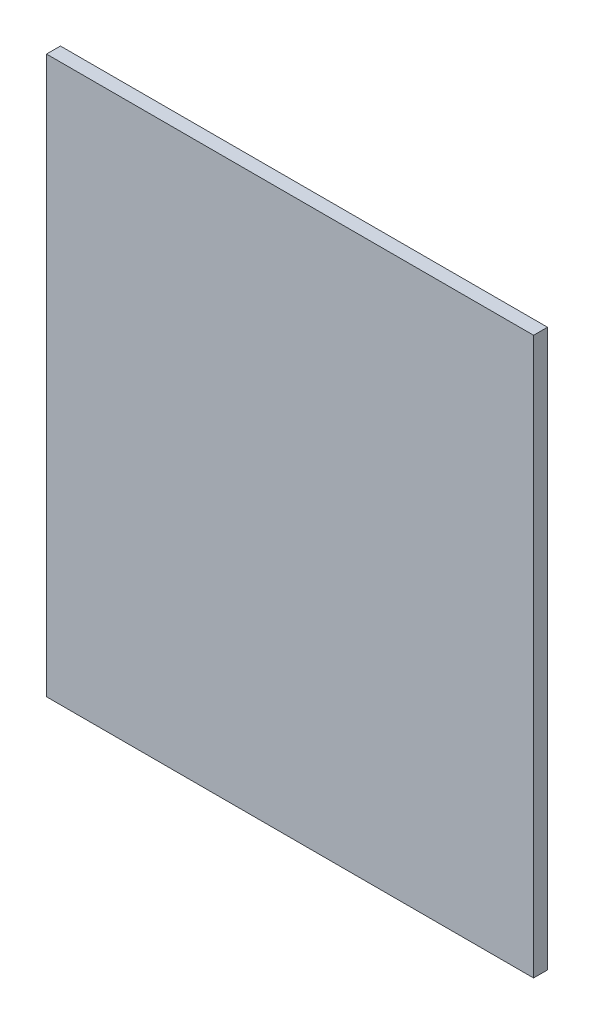
SolidWorks part; units mm, degrees
ref_plane "Front Plane" through (0, 0, 0) normal (1, 0, 0) x (0, 1, 0)
ref_plane "Top Plane" through (0, 0, 0) normal (0, 0, 1) x (0, 1, 0)
ref_plane "Right Plane" through (0, 0, 0) normal (0, 1, 0) x (-1, 0, 0)
sketch "Sketch1" plane through (0, 0, 0) normal (0, 0, 1) x (0, 1, 0)
  line L1 (0, 0) -> (101.6, 0)
  line L2 (0, 0) -> (0, 88.9)
  line L3 (0, 88.9) -> (101.6, 88.9)
  line L4 (101.6, 0) -> (101.6, 88.9)
  dimension "D1" = 88.9
  dimension "D2" = 101.6
extrude "Boss-Extrude1" add sketch "Sketch1" along normal blind 2.54
